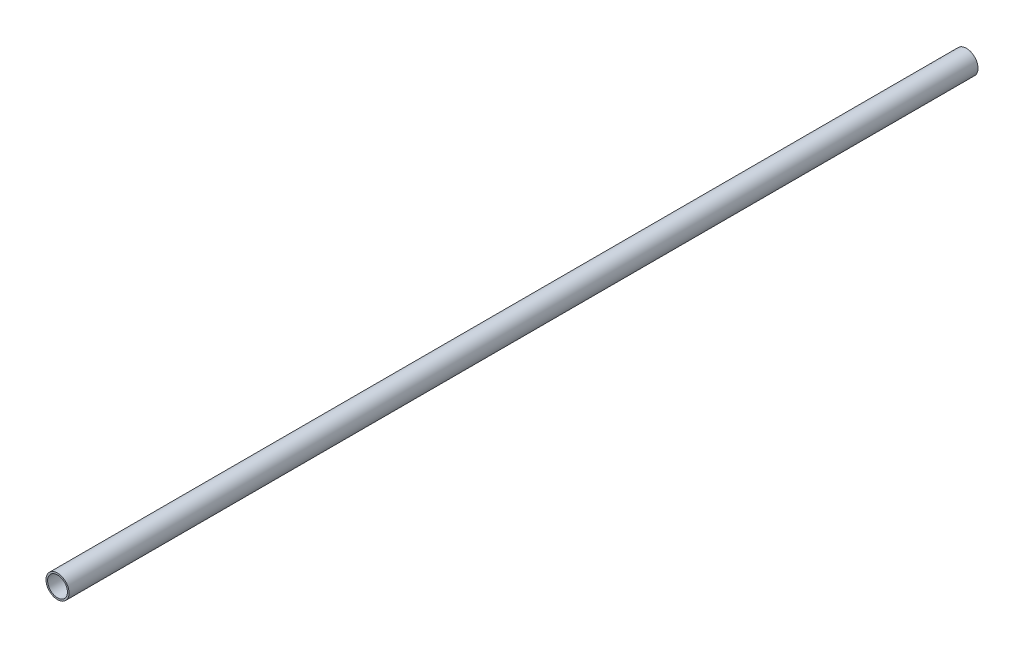
SolidWorks part; units mm, degrees
material "6063-T6, Rod (SS)"
ref_plane "Front Plane" through (0, 0, 0) normal (0, 0, 1) x (1, 0, 0)
ref_plane "Top Plane" through (0, 0, 0) normal (0, 1, 0) x (1, 0, 0)
ref_plane "Right Plane" through (0, 0, 0) normal (1, 0, 0) x (0, 0, -1)
sketch "Sketch1" plane through (0, 0, 0) normal (0, 0, 1) x (1, 0, 0)
  circle A0 centre (0, 0) radius 6.35
  circle A1 centre (0, 0) radius 5.461
  dimension "D1" = 12.7
  dimension "D2" = 10.922
extrude "Boss-Extrude1" add sketch "Sketch1" along normal blind 500
